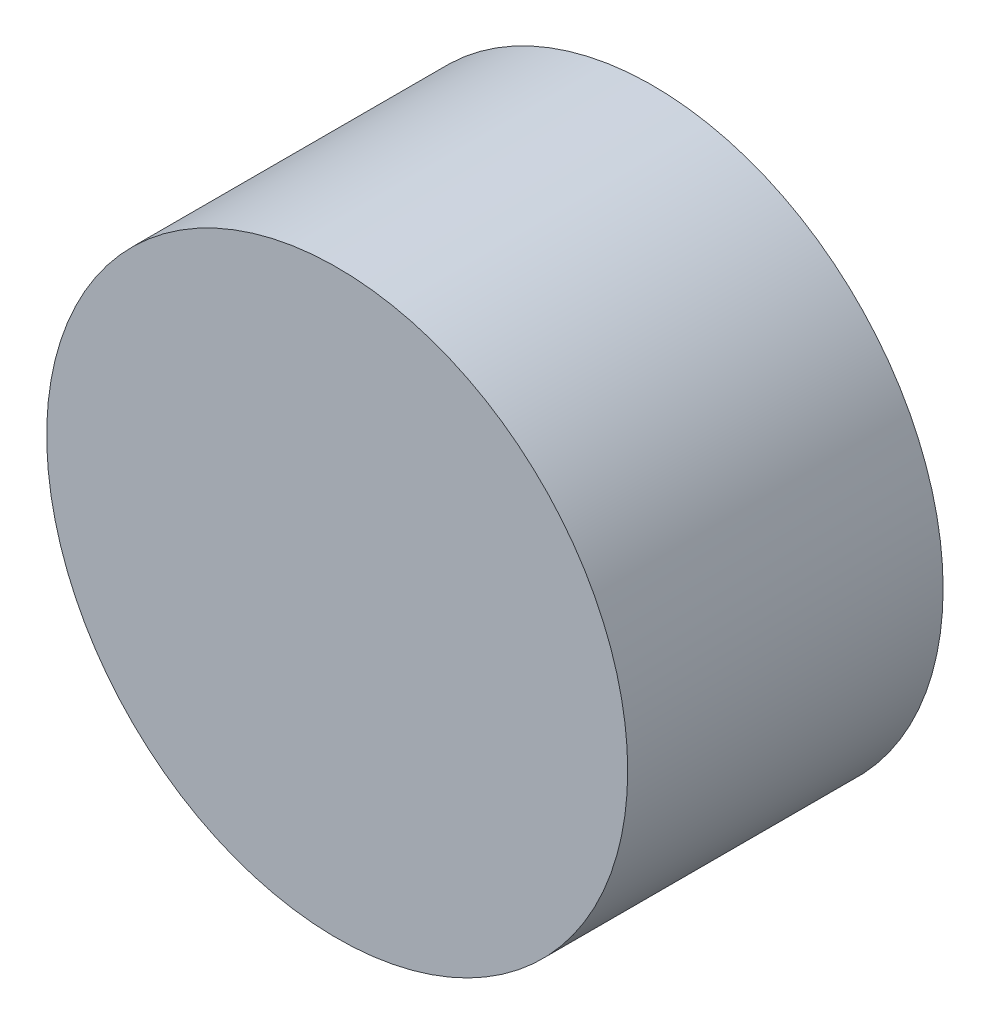
SolidWorks part; units mm, degrees
ref_plane "Plan de face" through (0, 0, 0) normal (0, 0, 1) x (1, 0, 0)
ref_plane "Plan de dessus" through (0, 0, 0) normal (0, 1, 0) x (1, 0, 0)
ref_plane "Plan de droite" through (0, 0, 0) normal (1, 0, 0) x (0, 0, -1)
sketch "Esquisse1" plane through (0, 0, 0) normal (0, 0, 1) x (1, 0, 0)
  circle A0 centre (86.6025, -15) radius 17.5 construction
  circle A1 centre (86.6025, -15) radius 17.5
extrude "Boss.-Extru.1" add sketch "Esquisse1" against normal blind 19
sketch "Esquisse2" plane through (0, 0, -19) normal (0, 0, -1) x (-1, 0, 0)
  circle A0 centre (-86.6025, -15) radius 16.5
  circle A1 centre (-86.6025, -15) radius 17.5 construction
  dimension "D1" = 1
extrude "Enlèv. mat.-Extru.1" cut sketch "Esquisse2" against normal blind 15
